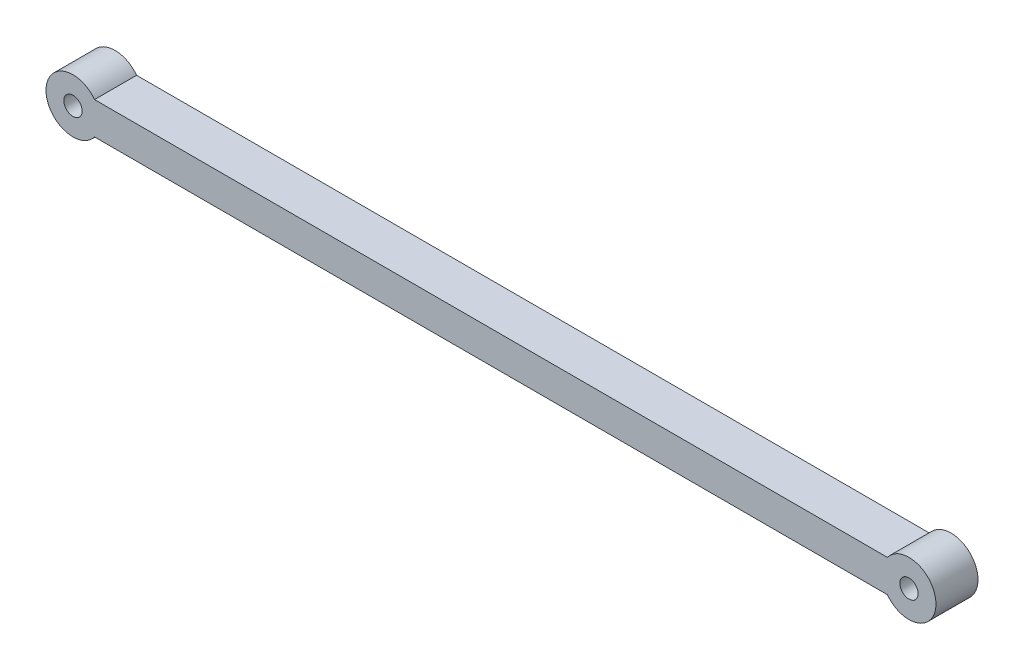
SolidWorks part; units mm, degrees
ref_plane "前视基准面" through (0, 0, 0) normal (0, 0, 1) x (1, 0, 0)
ref_plane "上视基准面" through (0, 0, 0) normal (0, 1, 0) x (1, 0, 0)
ref_plane "右视基准面" through (0, 0, 0) normal (1, 0, 0) x (0, 0, -1)
sketch "草图1" plane through (0, 0, 0) normal (0, 0, 1) x (1, 0, 0)
  line L0 (0, 50) -> (155, 50) construction
  line L1 (4, 53) -> (151, 53)
  line L2 (4, 47) -> (151, 47)
  arc A0 (4, 53) -> (4, 47) centre (0, 50) ccw
  circle A1 centre (0, 50) radius 1.7
  circle A2 centre (155, 50) radius 1.7
  arc A3 (151, 47) -> (151, 53) centre (155, 50) ccw
  dimension "D1" = 3
  dimension "D2" = 10
  dimension "D3" = 10
  dimension "D4" = 3.4
  dimension "D5" = 3.4
extrude "凸台-拉伸1" add sketch "草图1" along normal blind 7.8
